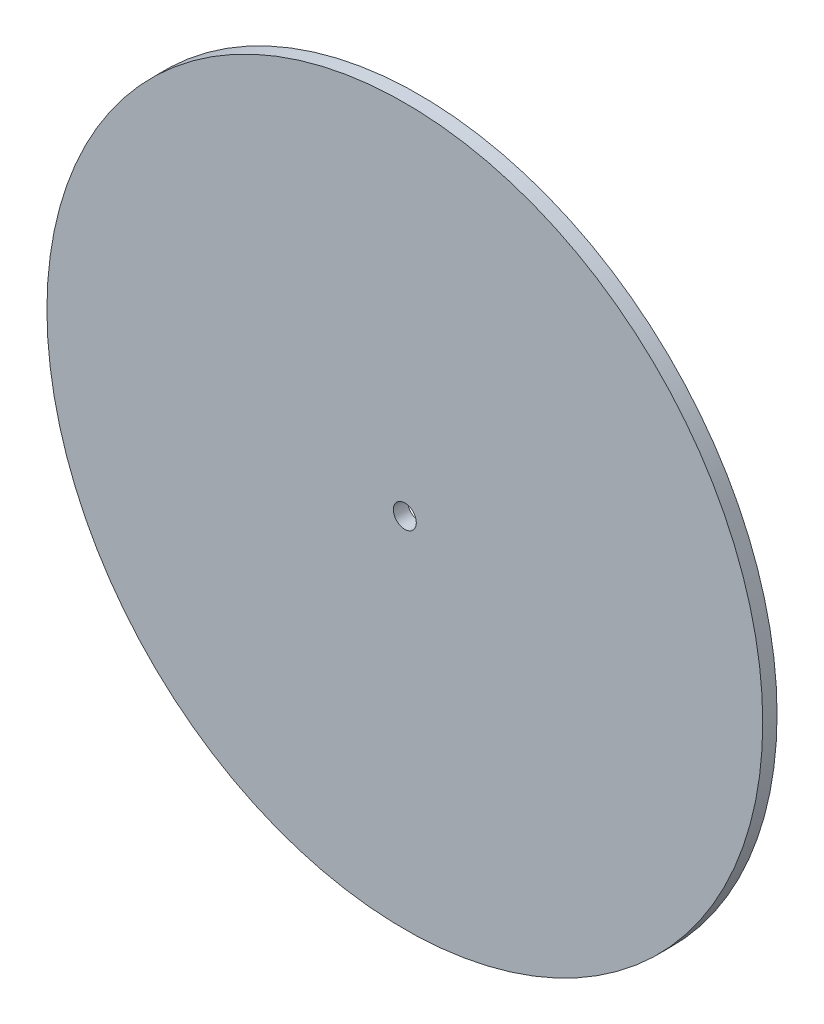
SolidWorks part; units mm, degrees
ref_plane "Front Plane" through (0, 0, 0) normal (0, 0, 1) x (1, 0, 0)
ref_plane "Top Plane" through (0, 0, 0) normal (0, 1, 0) x (1, 0, 0)
ref_plane "Right Plane" through (0, 0, 0) normal (1, 0, 0) x (0, 0, -1)
sketch "Sketch1" plane through (0, 0, 0) normal (0, 0, 1) x (1, 0, 0)
  circle A0 centre (0, 0) radius 2
  circle A1 centre (0, 0) radius 62.5
  dimension "D1" = 4
  dimension "D2" = 125
extrude "Boss-Extrude1" add sketch "Sketch1" along normal blind 2.5
